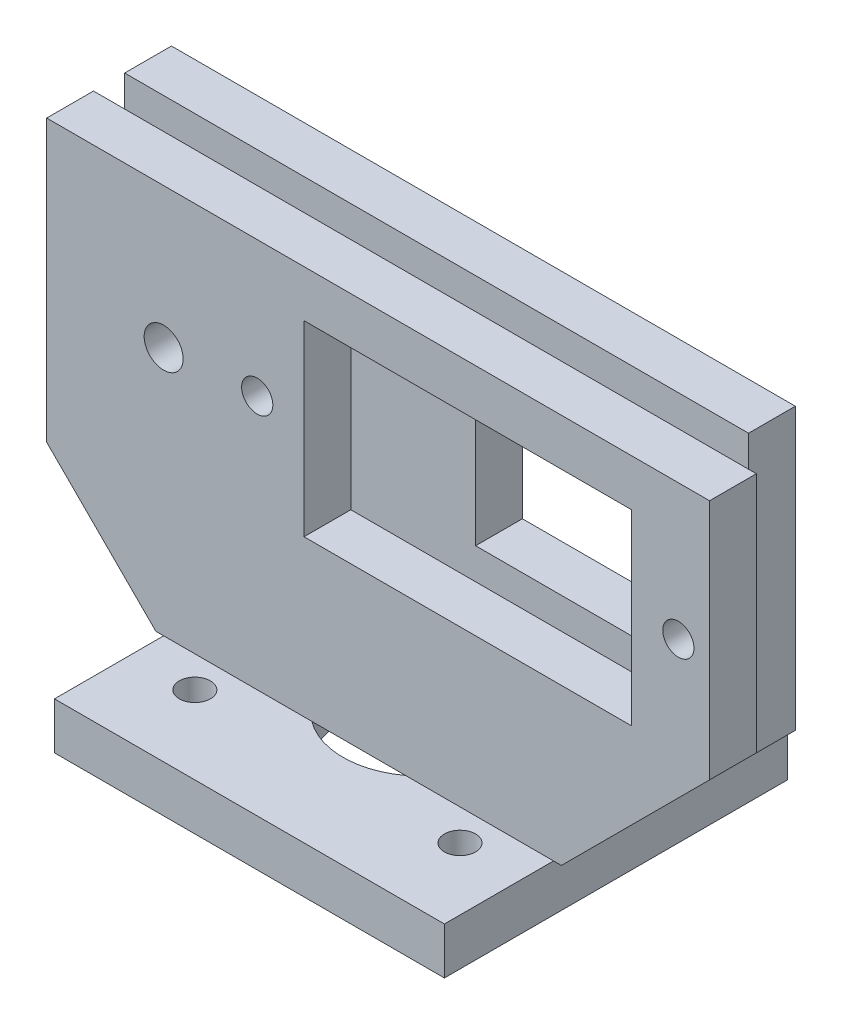
SolidWorks part; units mm, degrees
ref_plane "Front Plane" through (0, 0, 0) normal (0, 0, 1) x (1, 0, 0)
ref_plane "Top Plane" through (0, 0, 0) normal (0, 1, 0) x (1, 0, 0)
ref_plane "Right Plane" through (0, 0, 0) normal (1, 0, 0) x (0, 0, -1)
sketch "Sketch1" plane through (0, 0, 0) normal (0, 1, 0) x (1, 0, 0)
  line L0 (-19.4326, 0) -> (20.9456, 0) construction
  line L1 (0, 15.6738) -> (0, -16.7612) construction
  line L3 (-12.5, -11) -> (12.5, -11)
  line L4 (-12.5, -11) -> (-12.5, 11)
  line L5 (-12.5, 11) -> (12.5, 11)
  line L6 (12.5, -11) -> (12.5, 11)
  line L7 (-12.5, -11) -> (12.5, 11) construction
  line L8 (-12.5, 11) -> (12.5, -11) construction
  circle A0 centre (6, 8) radius 1
  circle A1 centre (-6, 8) radius 1
  circle A2 centre (0, 0) radius 5
  circle A3 centre (-8.5, -6) radius 1
  circle A4 centre (8.5, -6) radius 1
  point P8 (0, 0)
  dimension "D3" = 2
  dimension "D6" = 10
  dimension "D7" = 2
  dimension "D1" = 22
  dimension "D2" = 25
  dimension "D4" = 6
  dimension "D5" = 3
  dimension "D8" = 4
  dimension "D9" = 17
extrude "Boss-Extrude1" add sketch "Sketch1" along normal blind 3
sketch "Sketch2" plane through (0, 3, 0) normal (0, 1, 0) x (1, 0, 0)
  line L1 (-20, -4) -> (20, -4)
  line L2 (-20, -4) -> (-20, 4)
  line L3 (-20, 4) -> (20, 4)
  line L4 (20, -4) -> (20, 4)
  line L5 (-20, -4) -> (20, 4) construction
  line L6 (-20, 4) -> (20, -4) construction
  point P0 (0, 0)
  dimension "D1" = 8
  dimension "D2" = 40
extrude "Boss-Extrude2" add sketch "Sketch2" along normal blind 25
sketch "Sketch3" plane through (0, 28, 0) normal (0, 1, 0) x (1, 0, 0)
  line L0 (20, -4) -> (20, 4) construction
  line L1 (-20, -1) -> (20, -1)
  line L2 (-20, -1) -> (-20, 1)
  line L3 (-20, 1) -> (20, 1)
  line L4 (20, -1) -> (20, 1)
  line L5 (-20, -1) -> (20, 1) construction
  line L6 (-20, 1) -> (20, -1) construction
  line L7 (-12.5, 4) -> (-40, 4) construction
  point P0 (0, 0)
  dimension "D1" = 3
chamfer "Chamfer1" distance 7 angle 45 2 edges at (-20, 3, 0) (20, 3, 0)
extrude "Cut-Extrude1" cut sketch "Sketch3" against normal up to vertex (25 mm away)
sketch "Sketch7" plane through (0, 0, 4) normal (0, 0, 1) x (1, 0, 0)
  line L0 (0, 0) -> (0, 29.9236) construction
  line L1 (12.5, 31.0531) -> (12.5, -3.2369) construction
  line L2 (-3.5, 13) -> (17.5, 13)
  line L3 (-3.5, 13) -> (-3.5, 25)
  line L4 (-3.5, 25) -> (17.5, 25)
  line L5 (17.5, 13) -> (17.5, 25)
  line L6 (-3.5, 13) -> (17.5, 25) construction
  line L7 (-3.5, 25) -> (17.5, 13) construction
  line L8 (24.3693, 19) -> (-7.7483, 19) construction
  line L9 (3, 3) -> (12.5, 3) construction
  point P3 (7, 19)
  dimension "D1" = 12.5
  dimension "D2" = 5
  dimension "D3" = 16
  dimension "D4" = 16
  dimension "D5" = 12
extrude "Cut-Extrude2" cut sketch "Sketch7" against normal up to vertex (3 mm away)
sketch "Sketch8" plane through (0, 0, -1) normal (0, 0, 1) x (1, 0, 0)
  line L1 (17.5, 25) -> (2.5, 25)
  line L2 (17.5, 25) -> (17.5, 13)
  line L3 (17.5, 13) -> (2.5, 13)
  line L4 (2.5, 25) -> (2.5, 13)
  line L5 (-3.5, 13) -> (17.5, 13) construction
  point P5 (7.9607, 13)
  dimension "D1" = 15
extrude "Cut-Extrude3" cut sketch "Sketch8" against normal blind 31
sketch "Sketch9" plane through (0, 0, 4) normal (0, 0, 1) x (1, 0, 0)
  line L4 (-3.5, 19) -> (-12.5, 19) construction
  circle A0 centre (-12.5, 19) radius 1.25
  point P2 (-12.3248, 19)
  dimension "D2" = 2.5
  dimension "D1" = 12.5
extrude "Cut-Extrude4" cut sketch "Sketch9" against normal blind 31
sketch "Sketch10" plane through (0, 0, 4) normal (0, 0, 1) x (1, 0, 0)
  line L0 (20, 10) -> (22.5, 12.5)
  line L1 (20, 28) -> (22.5, 28)
  line L2 (20, 28) -> (20, 10)
  line L4 (22.5, 28) -> (22.5, 12.5)
  dimension "D1" = 2.5
extrude "Boss-Extrude3" add sketch "Sketch10" against normal up to vertex
sketch "Sketch11" plane through (0, 0, 4) normal (0, 0, 1) x (1, 0, 0)
  line L0 (-12.5, 19) -> (21.2697, 19.3191) construction
  line L1 (7, 25) -> (7, 11.8606) construction
  line L2 (17.5, 25) -> (-3.5, 25) construction
  circle A0 centre (20.5, 19.3119) radius 1
  circle A1 centre (-6.5, 19.3119) radius 1
  dimension "D2" = 2
  dimension "D1" = 13.5
extrude "Cut-Extrude5" cut sketch "Sketch11" against normal up to vertex (3 mm away)
